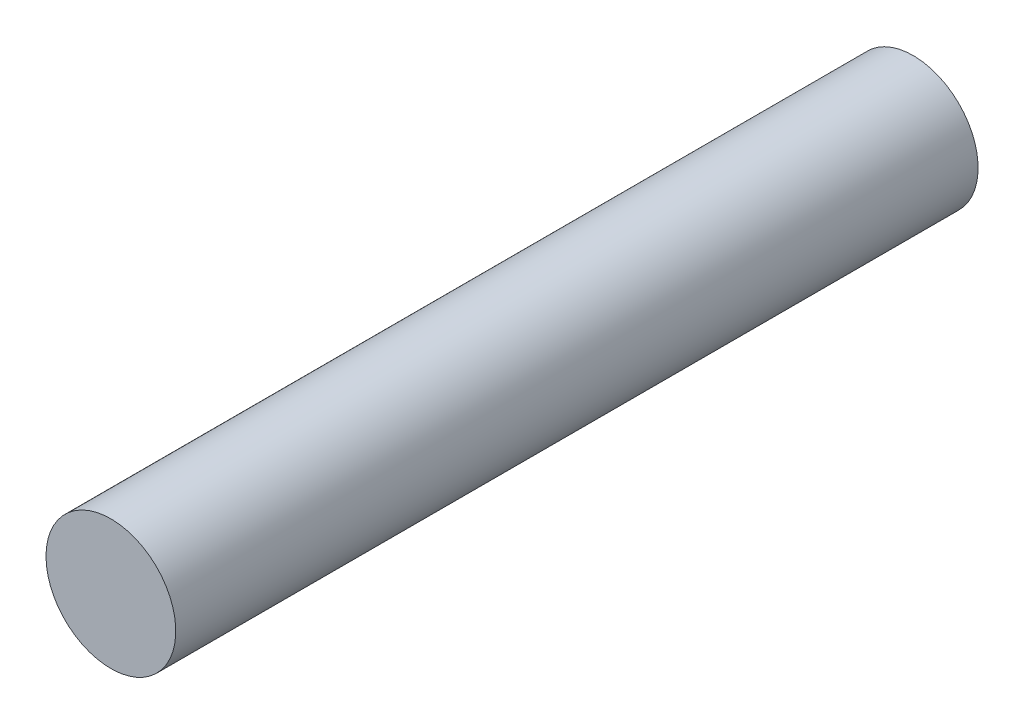
SolidWorks part; units mm, degrees
ref_plane "前视基准面" through (0, 0, 0) normal (0, 0, 1) x (1, 0, 0)
ref_plane "上视基准面" through (0, 0, 0) normal (0, 1, 0) x (1, 0, 0)
ref_plane "右视基准面" through (0, 0, 0) normal (1, 0, 0) x (0, 0, -1)
other "Configuration Table"
sketch "草图1" plane through (0, 0, 0) normal (0, 0, 1) x (1, 0, 0)
  line L0 (0, 0) -> (21, 0)
  arc A0 (0, 0) -> (21, 0) centre (10.5, 0) cw
  dimension "D1" = 21
extrude "凸台-拉伸2" add sketch "草图1" along normal blind 100
sketch "草图2" plane through (0, 0, 0) normal (0, 0, -1) x (-1, 0, 0)
  line L0 (0, 0) -> (-21, 0) construction
  circle A0 centre (-10.5, 0) radius 10.5117
extrude "凸台-拉伸3" add sketch "草图2" against normal blind 130
